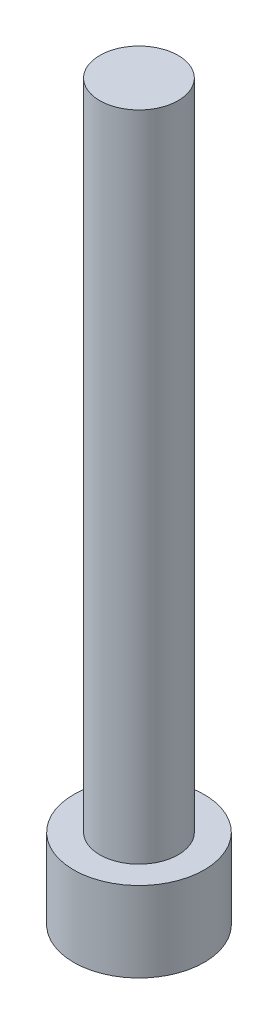
SolidWorks part; units mm, degrees
ref_plane "Front Plane" through (0, 0, 0) normal (0, 0, 1) x (1, 0, 0)
ref_plane "Top Plane" through (0, 0, 0) normal (0, 1, 0) x (1, 0, 0)
ref_plane "Right Plane" through (0, 0, 0) normal (1, 0, 0) x (0, 0, -1)
sketch "Sketch1" plane through (0, 0, 0) normal (0, 1, 0) x (1, 0, 0)
  circle A0 centre (0, 0) radius 2.8575
  dimension "D1" = 5.715
extrude "Boss-Extrude1" add sketch "Sketch1" along normal blind 3.5052
sketch "Sketch2" plane through (0, 0, 0) normal (0, -1, 0) x (1, 0, 0)
  line L1 (1.604, 0) -> (0.802, 1.3891)
  line L2 (0.802, 1.3891) -> (-0.802, 1.3891)
  line L3 (-0.802, 1.3891) -> (-1.604, 0)
  line L4 (-1.604, 0) -> (-0.802, -1.3891)
  line L5 (-0.802, -1.3891) -> (0.802, -1.3891)
  line L6 (0.802, -1.3891) -> (1.604, 0)
  circle A0 centre (0, 0) radius 1.3891 construction
  dimension "D1" = 2.7781
extrude "Cut-Extrude1" cut sketch "Sketch2" against normal blind 1.9558
sketch "Sketch3" plane through (0, 3.5052, 0) normal (0, 1, 0) x (1, 0, 0)
  circle A0 centre (0, 0) radius 1.7145
  dimension "D1" = 3.429
extrude "Boss-Extrude2" add sketch "Sketch3" along normal blind 28.575
